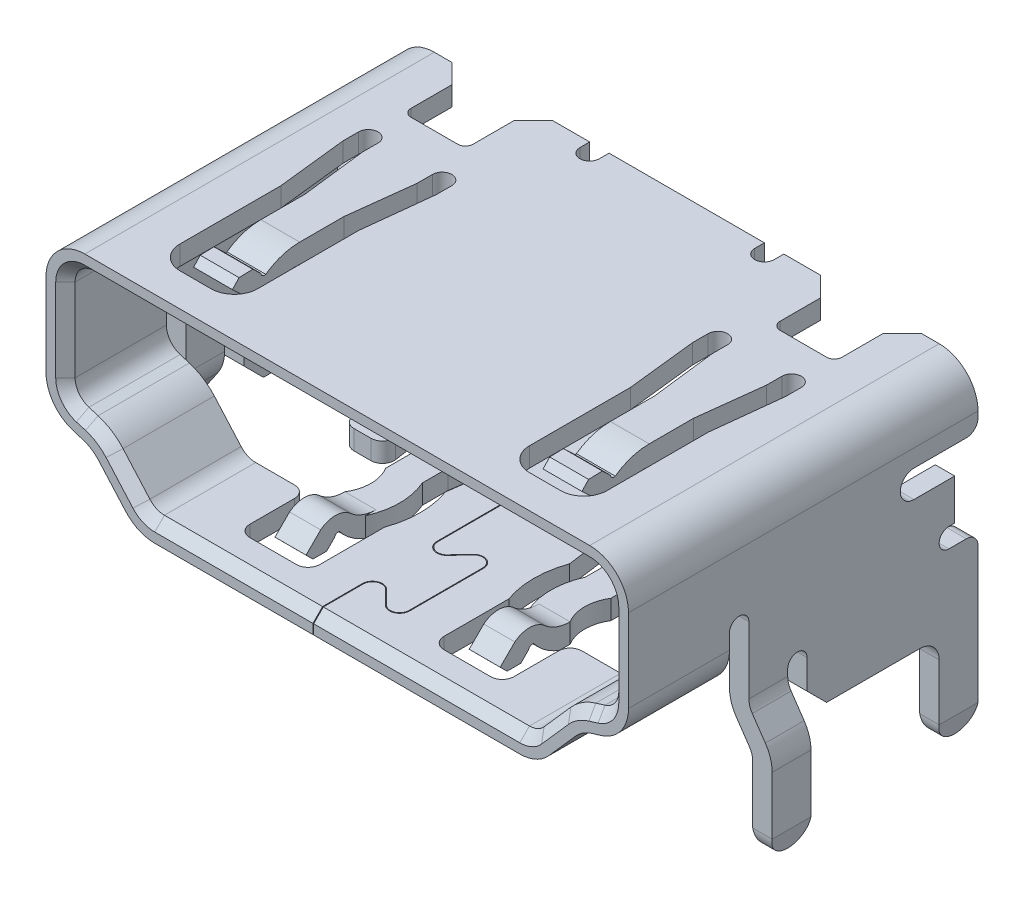
SolidWorks part; units mm, degrees
ref_plane "Front Plane" through (0, 0, 0) normal (0, 0, 1) x (1, 0, 0)
ref_plane "Top Plane" through (0, 0, 0) normal (0, 1, 0) x (1, 0, 0)
ref_plane "Right Plane" through (0, 0, 0) normal (1, 0, 0) x (0, 0, -1)
sketch "Esboço2" plane through (0, 0, 0) normal (0, 0, 1) x (1, 0, 0)
  line L0 (13.5, 2.775) -> (26.5, 2.775)
  line L1 (13.5, 2.275) -> (26.5, 2.275)
  line L2 (27.5, 1.775) -> (27.5, -0.36)
  line L3 (27, 1.775) -> (27, -0.36)
  line L4 (26.7905, -1.3169) -> (26.5535, -1.3888)
  line L5 (26.6453, -0.8384) -> (26.4083, -0.9104)
  line L6 (25.0749, -2.1059) -> (25.7654, -1.3236)
  line L7 (25.4497, -2.4367) -> (26.1402, -1.6544)
  line L8 (24.7, -2.275) -> (15.3, -2.275)
  line L9 (14.2346, -1.3236) -> (14.9251, -2.1059)
  line L10 (24.7, -2.775) -> (15.3, -2.775)
  line L11 (13.5917, -0.9104) -> (13.3547, -0.8384)
  line L12 (13, -0.36) -> (13, 1.775)
  line L13 (13.8598, -1.6544) -> (14.5503, -2.4367)
  line L16 (13.4465, -1.3888) -> (13.2095, -1.3169)
  line L18 (12.5, -0.36) -> (12.5, 1.775)
  arc A0 (26.5, 2.275) -> (27, 1.775) centre (26.5, 1.775) cw
  arc A1 (27, -0.36) -> (26.6453, -0.8384) centre (26.5, -0.36) cw
  arc A2 (26.4083, -0.9104) -> (25.7654, -1.3236) centre (26.815, -2.25) ccw
  arc A3 (24.7, -2.275) -> (25.0749, -2.1059) centre (24.7, -1.775) ccw
  arc A4 (15.3, -2.275) -> (14.9251, -2.1059) centre (15.3, -1.775) cw
  arc A5 (26.5535, -1.3888) -> (26.1402, -1.6544) centre (26.815, -2.25) ccw
  arc A6 (24.7, -2.775) -> (25.4497, -2.4367) centre (24.7, -1.775) ccw
  arc A7 (27.5, -0.36) -> (26.7905, -1.3169) centre (26.5, -0.36) cw
  arc A8 (12.5, -0.36) -> (13.2095, -1.3169) centre (13.5, -0.36) ccw
  arc A9 (13.4465, -1.3888) -> (13.8598, -1.6544) centre (13.185, -2.25) cw
  arc A10 (15.3, -2.775) -> (14.5503, -2.4367) centre (15.3, -1.775) cw
  arc A11 (26.5, 2.775) -> (27.5, 1.775) centre (26.5, 1.775) cw
  arc A12 (12.5, 1.775) -> (13.5, 2.775) centre (13.5, 1.775) cw
  arc A13 (13.5917, -0.9104) -> (14.2346, -1.3236) centre (13.185, -2.25) cw
  arc A14 (13, -0.36) -> (13.3547, -0.8384) centre (13.5, -0.36) ccw
  arc A15 (13, 1.775) -> (13.5, 2.275) centre (13.5, 1.775) cw
  dimension "D1" = 0.5
extrude "Ressalto-extrusão1" add sketch "Esboço2" along normal blind 8.3 and the other way blind 0.7 separate body
chamfer "Chanfro1" distance 0.25 angle 45 16 edges at (20, 2.275, 8.3) (13.1464, 2.1286, 8.3) (26.8536, 2.1286, 8.3) (13, 0.7075, 8.3) (27, 0.7075, 8.3) (13.0984, -0.6578, 8.3) (26.9016, -0.6578, 8.3) (13.4732, -0.8744, 8.3) (26.5268, -0.8744, 8.3) (13.9419, -1.0722, 8.3) (26.0581, -1.0722, 8.3) (14.5799, -1.7147, 8.3) (25.4201, -1.7147, 8.3) (15.0944, -2.2308, 8.3) (24.9056, -2.2308, 8.3) (20, -2.275, 8.3)
sketch "Esboço3" plane through (27.5, 0, 0) normal (1, 0, 0) x (0, 0, -1)
  line L1 (0.7, 2.775) -> (-8.3, 2.775) construction
  line L2 (-5.7, 0.025) -> (-5.7, -4.0402)
  line L3 (-5.7, -4.0402) -> (-5.2, -4.0402)
  line L4 (-5.2, 0.025) -> (-5.2, -0.225)
  line L5 (-8.3, -2.4367) -> (-8.3, -2.775) construction
  line L6 (-5.2, -0.225) -> (0.1, -0.225)
  line L7 (0.7, 1.775) -> (0.7, 1.625)
  line L8 (-5.2, -4.0402) -> (1.1225, -4.0402)
  line L9 (1.1225, -0.225) -> (1.1225, -4.0402)
  line L10 (0.7, -0.36) -> (0.7, 1.775) construction
  line L11 (0.7, 1.775) -> (1.1225, 1.775)
  line L12 (0.4, 1.325) -> (-0.95, 1.325)
  line L13 (1.1225, 1.775) -> (1.1225, -0.225)
  line L14 (-0.95, 0.625) -> (0.1, 0.625)
  line L15 (0.1, 0.625) -> (0.1, -0.225)
  arc A0 (-5.2, 0.025) -> (-5.7, 0.025) centre (-5.45, 0.025) ccw
  arc A1 (-0.95, 1.325) -> (-0.95, 0.625) centre (-0.95, 0.975) ccw
  arc A2 (0.4, 1.325) -> (0.7, 1.625) centre (0.4, 1.625) ccw
  dimension "D11" = 0.3
  dimension "D1" = 0.5
  dimension "D2" = 3
  dimension "D3" = 2.6
  dimension "D4" = 0.15
  dimension "D5" = 0.3
  dimension "D6" = 0.3
  dimension "D7" = 1.35
  dimension "D8" = 0.7
  dimension "D9" = 1.05
extrude "Corte-extrusão1" cut sketch "Esboço3" against normal blind 3
ref_plane "Plano1" through (20, 0, 0) normal (-1, 0, 0) x (0, 0, 1)
mirror "Espelhar1" about plane through (20, 0, 0) normal (-1, 0, 0) of "Corte-extrusão1"
sketch "Esboço6" plane through (27.5, 0, 0) normal (1, 0, 0) x (0, 0, -1)
  line L1 (0.1, -0.225) -> (0.1, -0.425)
  line L2 (0.1, -0.425) -> (-0.05, -0.425)
  line L3 (-3.2, -2.775) -> (-3.7, -2.275)
  line L4 (-0.05, -0.925) -> (0.4, -0.925)
  line L5 (-3.7, -2.275) -> (-3.7, -1.525)
  line L6 (0.7, -1.225) -> (0.7, -4.725)
  line L8 (-0.3, -4.725) -> (-0.3, -3.275)
  line L9 (-4.2, -1.525) -> (-4.2, -1.695)
  line L10 (-0.8, -2.775) -> (-3.2, -2.775)
  line L11 (-4.2, -1.695) -> (-5.2, -1.695)
  line L12 (-5.2, -1.0508) -> (-5.2, -0.225)
  line L13 (-5.2, -0.225) -> (0.1, -0.225)
  line L14 (-0.95, 0.625) -> (0.1, 0.625) construction
  line L15 (-5.2, -1.695) -> (-5.2, -1.0508)
  arc A0 (-0.05, -0.425) -> (-0.05, -0.925) centre (-0.05, -0.675) ccw
  arc A1 (0.4, -0.925) -> (0.7, -1.225) centre (0.4, -1.225) cw
  arc A2 (-0.3, -4.725) -> (0.7, -4.725) centre (0.2, -4.725) ccw
  arc A3 (-0.8, -2.775) -> (-0.3, -3.275) centre (-0.8, -3.275) cw
  arc A4 (-3.7, -1.525) -> (-4.2, -1.525) centre (-3.95, -1.525) ccw
  dimension "D7" = 0.3
  dimension "D14" = 0.5
  dimension "D1" = 1.05
  dimension "D2" = 0.15
  dimension "D3" = 0.5
  dimension "D4" = 0.45
  dimension "D5" = 0.3
  dimension "D6" = 0.3
  dimension "D8" = 3.5
  dimension "D9" = 1
  dimension "D10" = 1.45
  dimension "D11" = 0.5
  dimension "D12" = 0.5
  dimension "D13" = 2.4
  dimension "D15" = 0.5
  dimension "D16" = 0.5
  dimension "D17" = 0.75
  dimension "D18" = 0.5
  dimension "D19" = 0.17
extrude "Ressalto-extrusão3" add sketch "Esboço6" against normal blind 0.5
mirror "Espelhar2" about plane through (20, 0, 0) normal (-1, 0, 0) of "Ressalto-extrusão3"
sketch "Esboço8" plane through (0, 0, 5.2) normal (0, 0, 1) x (1, 0, 0)
  line L1 (27, -1.695) -> (27.5, -1.695) construction
  line L2 (27.381, -2.119) -> (27.718, -2.611)
  line L4 (27.849, -3.035) -> (27.849, -5.025)
  arc A0 (27.25, -1.695) -> (27.381, -2.119) centre (28, -1.6955) ccw
  arc A1 (27.718, -2.611) -> (27.849, -3.035) centre (27.099, -3.0345) cw
  dimension "D8" = 0.75
  dimension "D9" = 0.75
  dimension "D1" = 0.131
  dimension "D2" = 0.424
  dimension "D3" = 0.337
  dimension "D4" = 0.492
  dimension "D5" = 0.131
  dimension "D6" = 0.424
  dimension "D7" = 1.99
sketch "Esboço9" plane through (0, -1.695, 0) normal (0, -1, 0) x (1, 0, 0)
  line L1 (27, 5.2) -> (27.5, 5.2)
  line L2 (27, 5.2) -> (27, 4.2)
  line L3 (27, 4.2) -> (27.5, 4.2)
  line L4 (27.5, 5.2) -> (27.5, 4.2)
sweep "Varredura1" add profiles "Esboço9" path "Esboço8"
fillet "Filete1" radius 0.499 2 edges at (27.849, -5.025, 4.2) (27.849, -5.025, 5.2)
mirror "Espelhar3" about plane through (20, 0, 0) normal (-1, 0, 0) of "Filete1", "Varredura1"
sketch "Esboço10" plane through (0, 2.775, 0) normal (0, 1, 0) x (1, 0, 0)
  line L0 (26.5, 0.7) -> (26.5, -8.3) construction
  line L1 (26.5, 0.7) -> (13.5, 0.7) construction
  line L2 (26.05, 0.7) -> (25.55, 0.2)
  line L3 (25.55, 0.2) -> (25.55, -0.85)
  line L4 (22, 0.45) -> (22, 1.8258)
  line L5 (25.35, -1.05) -> (24.15, -1.05)
  line L6 (22, 1.8258) -> (26.05, 1.8258)
  line L7 (23.95, -0.85) -> (23.95, 0.2)
  line L8 (23.95, 0.2) -> (23.45, 0.7)
  line L9 (23.45, 0.7) -> (22.5, 0.7)
  line L10 (22.5, 0.7) -> (22.5, 0.45)
  line L11 (26.05, 1.8258) -> (26.05, 0.7)
  line L12 (24.1, -7.45) -> (24.9, -7.45)
  line L13 (23.5, -6.85) -> (23.5, -4.25)
  line L15 (25.5, -6.85) -> (25.5, -4.25)
  line L16 (26.5, -8.3) -> (13.5, -8.3) construction
  line L18 (25.5, -4.25) -> (25.7, -2.45)
  line L19 (24, -4.25) -> (24, -5.2673)
  line L20 (24, -5.2673) -> (25, -5.2673)
  line L21 (25, -4.25) -> (25, -5.2673)
  line L22 (23.5, -4.25) -> (23.3, -2.45)
  line L23 (25.7, -2.45) -> (25.7, -2.05)
  line L24 (23.3, -2.45) -> (23.3, -2.05)
  line L25 (25.2, -2.05) -> (25.2, -2.45)
  line L26 (25.2, -2.45) -> (25, -4.13)
  line L27 (25, -4.13) -> (25, -4.25)
  line L29 (23.8, -2.05) -> (23.8, -2.45)
  line L30 (23.8, -2.45) -> (24, -4.13)
  line L31 (24, -4.13) -> (24, -4.25)
  arc A0 (22, 0.45) -> (22.5, 0.45) centre (22.25, 0.45) ccw
  arc A1 (25.35, -1.05) -> (25.55, -0.85) centre (25.35, -0.85) ccw
  arc A2 (24.15, -1.05) -> (23.95, -0.85) centre (24.15, -0.85) cw
  arc A4 (24.1, -7.45) -> (23.5, -6.85) centre (24.1, -6.85) cw
  arc A5 (24.9, -7.45) -> (25.5, -6.85) centre (24.9, -6.85) ccw
  arc A6 (25.7, -2.05) -> (25.2, -2.05) centre (25.45, -2.05) ccw
  arc A7 (23.8, -2.05) -> (23.3, -2.05) centre (23.55, -2.05) ccw
  point P29 (23.5, -7.45)
  point P32 (25.5, -7.45)
  dimension "D13" = 0.2
  dimension "D14" = 0.2
  dimension "D19" = 0.6
  dimension "D2" = 0.5
  dimension "D3" = 0.5
  dimension "D4" = 1.05
  dimension "D5" = 0.2
  dimension "D6" = 0.2
  dimension "D7" = 1.05
  dimension "D8" = 0.5
  dimension "D9" = 1.2
  dimension "D10" = 0.95
  dimension "D11" = 0.25
  dimension "D12" = 0.5
  dimension "D15" = 1
  dimension "D16" = 0.85
  dimension "D17" = 2
  dimension "D18" = 3.2
  dimension "D20" = 3.0327
  dimension "D21" = 1
  dimension "D22" = 0.5
  dimension "D23" = 0.2
  dimension "D24" = 1.8
  dimension "D25" = 0.5
  dimension "D26" = 0.4
  dimension "D27" = 0.4
  dimension "D28" = 1.68
  dimension "D29" = 1.8
  dimension "D30" = 0.4
  dimension "D31" = 0.5
  dimension "D32" = 0.4
  dimension "D33" = 1.68
  dimension "D34" = 0.2
extrude "Corte-extrusão2" cut sketch "Esboço10" against normal blind 1
mirror "Espelhar4" about plane through (20, 0, 0) normal (-1, 0, 0) of "Corte-extrusão2"
sketch "Esboço11" plane through (0, -2.775, 0) normal (0, -1, 0) x (1, 0, 0)
  line L0 (15.5, 5.7) -> (16.3, 5.7)
  line L1 (17.1, 4.1529) -> (17.1, 3.3272)
  line L2 (16.6, 6) -> (16.6, 7.15)
  line L3 (17.9, 5.4748) -> (17.1, 5.4748)
  line L4 (16.9, 7.45) -> (18.1, 7.45)
  line L5 (17.1, 5.4748) -> (17.1, 5.2048)
  line L6 (18.4, 7.15) -> (18.4, 5.482)
  line L7 (17.1, 3.3272) -> (16.9105, 1.9257)
  line L8 (18.4, 3.918) -> (18.6, 2.45)
  line L9 (18.6, 2.45) -> (18.6, 1.95)
  line L10 (18.3106, 0.0757) -> (20, 0.0757)
  line L11 (18.1, 1.95) -> (17.9, 3.35)
  line L12 (17.9, 3.35) -> (17.9, 4.01)
  line L13 (16.4105, 1.9257) -> (16.4105, 2.4257)
  line L14 (16.4105, 2.4257) -> (16.5376, 3.3341)
  line L15 (20, 3.85) -> (20, -3.85) construction
  line L16 (16.2405, 3.6757) -> (15.8106, 3.6757)
  line L17 (20, 0.0757) -> (20, -1.1005)
  line L18 (15.5106, 3.3757) -> (15.5106, 1.3757)
  line L19 (15.5106, 1.3757) -> (16.0106, 0.8757)
  line L20 (16.0106, 0.8757) -> (17.7106, 0.8757)
  line L21 (20, -1.1005) -> (14.9193, -1.1005)
  line L22 (18.0106, 0.5757) -> (18.0106, 0.3757)
  line L23 (14.9193, -1.1005) -> (14.9193, 5.2048)
  line L24 (14.9193, 5.2048) -> (15.5, 5.7)
  arc A0 (16.3, 5.7) -> (16.6, 6) centre (16.3, 6) ccw
  arc A1 (16.9, 7.45) -> (16.6, 7.15) centre (16.9, 7.15) ccw
  arc A2 (18.1, 7.45) -> (18.4, 7.15) centre (18.1, 7.15) cw
  arc A3 (18.4, 3.918) -> (18.4, 5.482) centre (16.237, 4.7) ccw
  arc A4 (18.1, 1.95) -> (18.6, 1.95) centre (18.35, 1.95) ccw
  arc A5 (17.9, 5.4748) -> (17.9, 4.01) centre (16.2557, 4.7424) cw
  arc A6 (17.1, 4.1529) -> (17.1, 5.2048) centre (16.2495, 4.6788) ccw
  arc A7 (16.4105, 1.9257) -> (16.9105, 1.9257) centre (16.6605, 1.9257) ccw
  arc A8 (16.5376, 3.3341) -> (16.2405, 3.6757) centre (16.2405, 3.3757) ccw
  arc A9 (15.8106, 3.6757) -> (15.5106, 3.3757) centre (15.8106, 3.3757) ccw
  arc A10 (17.7106, 0.8757) -> (18.0106, 0.5757) centre (17.7106, 0.5757) cw
  arc A11 (18.0106, 0.3757) -> (18.3106, 0.0757) centre (18.3106, 0.3757) ccw
  dimension "D17" = 0.3
  dimension "D18" = 0.3
  dimension "D19" = 2.3
  dimension "D21" = 1.8
  dimension "D25" = 1
  dimension "D35" = 0.3
  dimension "D46" = 0.3
  dimension "D47" = 0.3
  dimension "D48" = 0.3
  dimension "D1" = 1
  dimension "D2" = 0.3
  dimension "D3" = 0.3
  dimension "D4" = 1.15
  dimension "D5" = 0.3
  dimension "D6" = 1.2
  dimension "D7" = 0.3
  dimension "D8" = 1.668
  dimension "D9" = 1.564
  dimension "D10" = 1.468
  dimension "D11" = 0.2
  dimension "D12" = 0.5
  dimension "D13" = 0.5
  dimension "D14" = 0.2
  dimension "D15" = 1.4
  dimension "D16" = 0.66
  dimension "D20" = 1.4648
  dimension "D22" = 0.8
  dimension "D23" = 0.27
  dimension "D24" = 1.0519
  dimension "D26" = 0.8257
  dimension "D27" = 0.1895
  dimension "D28" = 1.4015
  dimension "D29" = 0.5
  dimension "D30" = 0.5
  dimension "D31" = 0.1271
  dimension "D32" = 0.9084
  dimension "D33" = 0.2971
  dimension "D34" = 0.3416
  dimension "D36" = 0.4299
  dimension "D37" = 0.3
  dimension "D38" = 0.3
  dimension "D39" = 2
  dimension "D40" = 0.5
  dimension "D41" = 0.5
  dimension "D42" = 1.7
  dimension "D43" = 0.3
  dimension "D44" = 0.2
  dimension "D45" = 0.3
extrude "Corte-extrusão3" cut sketch "Esboço11" against normal blind 1
mirror "Espelhar5" about plane through (20, 0, 0) normal (-1, 0, 0) of "Corte-extrusão3"
sketch "Esboço12" plane through (0, -2.775, 0) normal (0, -1, 0) x (1, 0, 0)
  line L0 (19.4006, -0.1177) -> (19.4006, 1.3257) construction
  line L1 (19.4106, -0.1177) -> (19.4106, 1.3257)
  line L2 (19.8291, 1.5007) -> (20.172, 1.1508) construction
  line L3 (20.172, 3.4008) -> (19.8291, 3.0509) construction
  line L4 (20.6005, 1.3258) -> (20.6005, 3.2258) construction
  line L5 (18.0106, 0.3757) -> (18.0106, 0.5757) construction
  line L6 (19.822, 1.4937) -> (20.1649, 1.1438)
  line L7 (19.4006, 3.2259) -> (19.4006, 5.1259) construction
  line L8 (20.6105, 1.3258) -> (20.6105, 3.2258)
  line L9 (19.8291, 5.3009) -> (20.154, 4.951) construction
  line L10 (20.1649, 3.4078) -> (19.822, 3.0579)
  line L11 (20.5825, 5.126) -> (20.5825, 7.026) construction
  line L12 (19.4106, 3.2259) -> (19.4106, 5.1259)
  line L13 (20.154, 7.201) -> (19.8111, 6.8511) construction
  line L14 (19.8219, 5.294) -> (20.1468, 4.9441)
  line L15 (19.3826, 7.0261) -> (19.3826, 9.0658) construction
  line L16 (21.6894, 0.0757) -> (18.3106, 0.0757) construction
  line L17 (20.5925, 5.126) -> (20.5925, 7.026)
  line L18 (20.1469, 7.208) -> (19.804, 6.8581)
  line L19 (19.3926, 7.0261) -> (19.3926, 9.0658)
  line L20 (19.3906, -0.1177) -> (19.3906, 1.3257)
  line L21 (19.8362, 1.5077) -> (20.1791, 1.1578)
  line L22 (20.5905, 1.3258) -> (20.5905, 3.2258)
  line L23 (20.1791, 3.3938) -> (19.8362, 3.0439)
  line L24 (19.3906, 3.2259) -> (19.3906, 5.1259)
  line L25 (19.8363, 5.3078) -> (20.1613, 4.9579)
  line L26 (20.5725, 5.126) -> (20.5725, 7.026)
  line L27 (20.1612, 7.194) -> (19.8183, 6.8441)
  line L28 (19.3726, 7.0261) -> (19.3726, 9.0658)
  arc A0 (19.8291, 1.5007) -> (19.4006, 1.3257) centre (19.6506, 1.3257) ccw construction
  arc A1 (20.172, 1.1508) -> (20.6005, 1.3258) centre (20.3505, 1.3258) ccw construction
  arc A2 (19.8291, 3.0509) -> (19.4006, 3.2259) centre (19.6506, 3.2259) cw construction
  arc A3 (20.172, 3.4008) -> (20.6005, 3.2258) centre (20.3505, 3.2258) cw construction
  arc A4 (19.8291, 5.3009) -> (19.4006, 5.1259) centre (19.6506, 5.1259) ccw construction
  arc A5 (20.154, 4.951) -> (20.5825, 5.126) centre (20.3325, 5.126) ccw construction
  arc A6 (19.8111, 6.8511) -> (19.3826, 7.0261) centre (19.6326, 7.0261) cw construction
  arc A7 (20.154, 7.201) -> (20.5825, 7.026) centre (20.3325, 7.026) cw construction
  arc A8 (19.822, 1.4937) -> (19.4106, 1.3257) centre (19.6506, 1.3257) ccw
  arc A9 (20.1649, 1.1438) -> (20.6105, 1.3258) centre (20.3505, 1.3258) ccw
  arc A10 (20.1649, 3.4078) -> (20.6105, 3.2258) centre (20.3505, 3.2258) cw
  arc A11 (19.822, 3.0579) -> (19.4106, 3.2259) centre (19.6506, 3.2259) cw
  arc A12 (19.8219, 5.294) -> (19.4106, 5.1259) centre (19.6506, 5.1259) ccw
  arc A13 (20.1468, 4.9441) -> (20.5925, 5.126) centre (20.3325, 5.126) ccw
  arc A14 (20.1469, 7.208) -> (20.5925, 7.026) centre (20.3325, 7.026) cw
  arc A15 (19.804, 6.8581) -> (19.3926, 7.0261) centre (19.6326, 7.0261) cw
  arc A16 (19.8362, 1.5077) -> (19.3906, 1.3257) centre (19.6506, 1.3257) ccw
  arc A17 (20.1791, 1.1578) -> (20.5905, 1.3258) centre (20.3505, 1.3258) ccw
  arc A18 (20.1791, 3.3938) -> (20.5905, 3.2258) centre (20.3505, 3.2258) cw
  arc A19 (19.8362, 3.0439) -> (19.3906, 3.2259) centre (19.6506, 3.2259) cw
  arc A20 (19.8363, 5.3078) -> (19.3906, 5.1259) centre (19.6506, 5.1259) ccw
  arc A21 (20.1613, 4.9579) -> (20.5725, 5.126) centre (20.3325, 5.126) ccw
  arc A22 (20.1612, 7.194) -> (20.5725, 7.026) centre (20.3325, 7.026) cw
  arc A23 (19.8183, 6.8441) -> (19.3726, 7.0261) centre (19.6326, 7.0261) cw
  arc A24 (19.4106, -0.1177) -> (19.3906, -0.1177) centre (19.4006, -0.1177) cw
  arc A25 (19.3926, 9.0658) -> (19.3726, 9.0658) centre (19.3826, 9.0658) ccw
  dimension "D9" = 0.25
  dimension "D10" = 0.25
  dimension "D30" = 0.25
  dimension "D31" = 0.25
  dimension "D32" = 0.25
  dimension "D33" = 0.25
  dimension "D34" = 0.25
  dimension "D35" = 0.25
  dimension "D1" = 1.39
  dimension "D2" = 0.4285
  dimension "D3" = 0.175
  dimension "D4" = 0.3429
  dimension "D5" = 0.3499
  dimension "D6" = 0.4285
  dimension "D7" = 0.175
  dimension "D8" = 1.9
  dimension "D11" = 0.175
  dimension "D12" = 0.3499
  dimension "D13" = 0.4285
  dimension "D14" = 0.4285
  dimension "D15" = 0.3429
  dimension "D16" = 1.9
  dimension "D17" = 0.175
  dimension "D18" = 0.175
  dimension "D19" = 0.175
  dimension "D20" = 0.175
  dimension "D21" = 0.175
  dimension "D22" = 0.3499
  dimension "D23" = 0.3499
  dimension "D24" = 1.9
  dimension "D25" = 0.4285
  dimension "D26" = 0.4285
  dimension "D27" = 0.4285
  dimension "D28" = 0.3429
  dimension "D29" = 1.25
  dimension "D36" = 0.01
  dimension "D37" = 0.01
extrude "Corte-extrusão4" cut sketch "Esboço12" against normal blind 1
sketch "Esboço14" plane through (22.9, 0, 0) normal (1, 0, 0) x (0, 0, -1)
  line L0 (-5.2048, -2.275) -> (-5.2048, -2.775)
  line L1 (-5.2048, -2.775) -> (-5.4748, -2.775)
  line L2 (-6.627, -2.0125) -> (-7.0036, -2.3876)
  line L3 (-7.0036, -2.3876) -> (-6.8272, -2.5647)
  line L4 (-6.8272, -2.5647) -> (-6.4736, -2.5647)
  line L5 (-6.4736, -2.5647) -> (-6.2742, -2.366)
  arc A0 (-5.2048, -2.275) -> (-5.829, -2.0562) centre (-5.2047, -1.275) cw
  arc A1 (-6.627, -2.0125) -> (-5.829, -2.0562) centre (-6.2525, -2.4813) cw
  arc A2 (-6.2742, -2.366) -> (-6.1412, -2.293) centre (-6.1763, -2.3866) cw
  arc A3 (-6.1412, -2.293) -> (-5.4748, -2.775) centre (-4.9626, -1.3652) ccw
  dimension "D14" = 1
  dimension "D15" = 0.6
  dimension "D16" = 0.1
  dimension "D17" = 1.5
  dimension "D1" = 0.2188
  dimension "D2" = 0.6242
  dimension "D3" = 0.798
  dimension "D4" = 0.0437
  dimension "D5" = 0.3766
  dimension "D6" = 0.3751
  dimension "D7" = 0.1764
  dimension "D8" = 0.1771
  dimension "D9" = 0.3536
  dimension "D10" = 0.1994
  dimension "D11" = 0.1987
  dimension "D12" = 0.073
  dimension "D13" = 0.133
extrude "Ressalto-extrusão4" add sketch "Esboço14" against normal blind 0.8
sketch "Esboço15" plane through (25, 0, 0) normal (1, 0, 0) x (0, 0, -1)
  line L0 (-5.2673, 2.275) -> (-5.2673, 2.775)
  line L2 (-6.2686, 2.5787) -> (-6.475, 2.7735)
  line L3 (-6.475, 2.7735) -> (-6.8284, 2.7633)
  line L4 (-6.8284, 2.7633) -> (-7, 2.5815)
  line L5 (-7, 2.5815) -> (-6.6118, 2.2151)
  line L7 (0.7, 2.275) -> (-8.05, 2.275) construction
  arc A0 (-6.1417, 2.4937) -> (-6.2686, 2.5787) centre (-6.1692, 2.5898) cw
  arc A1 (-5.2673, 2.775) -> (-6.1417, 2.4937) centre (-5.2672, 1.275) ccw
  arc A2 (-5.8502, 2.164) -> (-6.6118, 2.2151) centre (-6.2, 2.6515) cw
  arc A3 (-5.8502, 2.164) -> (-5.2673, 2.275) centre (-5.3801, 1.2814) cw
  dimension "D15" = 0.1
  dimension "D16" = 1.5
  dimension "D17" = 0.6
  dimension "D18" = 1
  dimension "D1" = 0.8744
  dimension "D2" = 0.1269
  dimension "D3" = 0.2064
  dimension "D4" = 0.3534
  dimension "D5" = 0.1716
  dimension "D6" = 0.3882
  dimension "D7" = 0.7616
  dimension "D8" = 0.2813
  dimension "D9" = 0.085
  dimension "D10" = 0.1948
  dimension "D11" = 0.0102
  dimension "D12" = 0.1818
  dimension "D13" = 0.3664
  dimension "D14" = 0.0511
extrude "Ressalto-extrusão5" add sketch "Esboço15" against normal blind 1
mirror "Espelhar6" about plane through (20, 0, 0) normal (-1, 0, 0) of "Ressalto-extrusão5", "Ressalto-extrusão4"
sketch "Esboço16" plane through (0, 0, 5.2) normal (0, 0, 1) x (1, 0, 0)
  line L0 (28.099, -4.526) -> (27.999, -5.025)
  line L1 (28.099, -5.025) -> (27.599, -5.025) construction
  line L2 (27.699, -5.025) -> (27.999, -5.025)
  line L3 (28.2403, -4.526) -> (28.2403, -5.3798)
  line L5 (28.2403, -4.526) -> (28.099, -4.526)
  line L6 (27.599, -4.526) -> (27.699, -5.025)
  line L7 (27.5553, -4.526) -> (27.5, -4.725)
  line L8 (27.5, -3.275) -> (27.5, -4.725) construction
  line L9 (27.5, -4.725) -> (27.4, -5.225)
  line L10 (27.5553, -4.526) -> (27.599, -4.526)
  line L11 (27, -5.225) -> (27.5, -5.225) construction
  line L12 (27.4, -5.225) -> (27.1, -5.225)
  line L13 (27.1, -5.225) -> (27, -4.725)
  line L14 (27, -4.725) -> (26.8152, -4.725)
  line L15 (26.8152, -4.725) -> (26.8152, -5.3798)
  line L16 (26.8152, -5.3798) -> (28.2403, -5.3798)
  dimension "D1" = 0.1
  dimension "D2" = 0.1
  dimension "D3" = 0.1
  dimension "D4" = 0.1
extrude "Corte-extrusão5" cut sketch "Esboço16" against normal blind 11
mirror "Espelhar7" about plane through (20, 0, 0) normal (-1, 0, 0) of "Corte-extrusão5"
